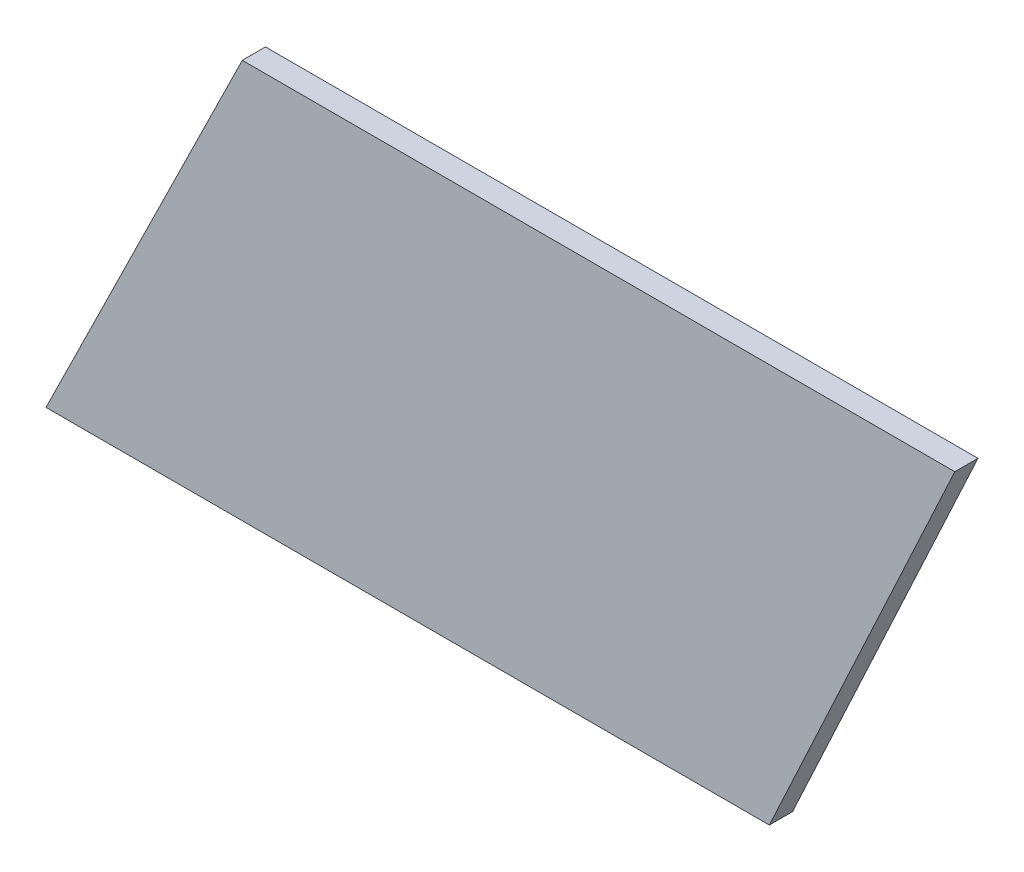
SolidWorks part; units mm, degrees
ref_plane "Front Plane" through (0, 0, 0) normal (0, 0, 1) x (1, 0, 0)
ref_plane "Top Plane" through (0, 0, 0) normal (0, 1, 0) x (1, 0, 0)
ref_plane "Right Plane" through (0, 0, 0) normal (1, 0, 0) x (0, 0, -1)
sketch "Sketch1" plane through (0, 0, 0) normal (0, 0, 1) x (1, 0, 0)
  line L0 (0, 0) -> (12, 25.8)
  line L1 (12, 25.8) -> (-34.1, 25.8)
  line L2 (-34.1, 25.8) -> (-46.8, 0)
  line L3 (-46.8, 0) -> (0, 0)
  dimension "D1" = 46.8
  dimension "D2" = 46.1
  dimension "D3" = 25.8
  dimension "D4" = 12.7
extrude "Boss-Extrude1" add sketch "Sketch1" along normal blind 1.5
